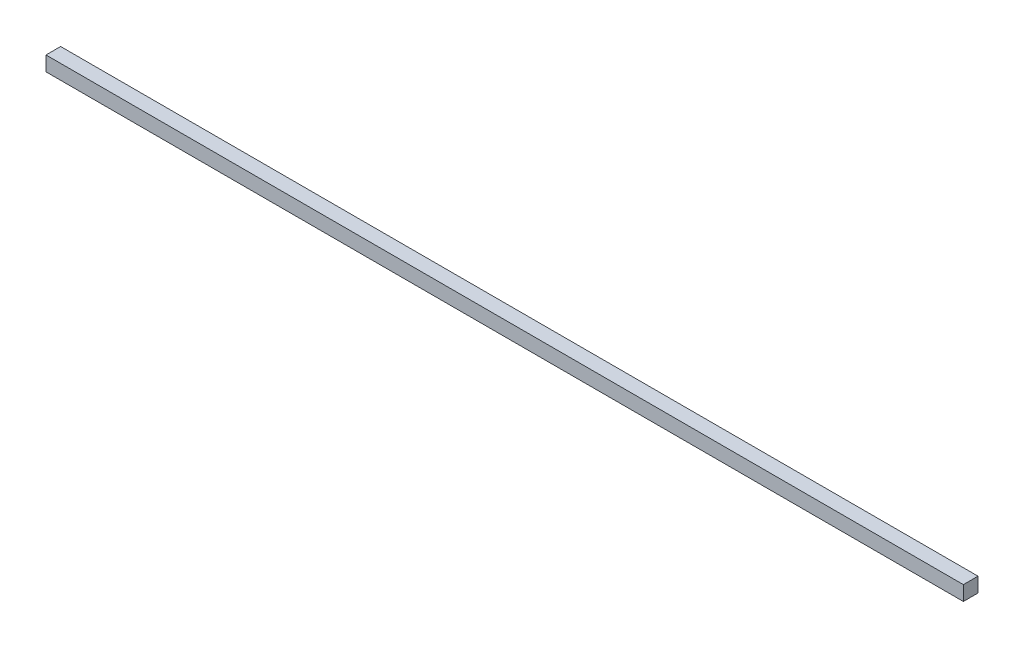
SolidWorks part; units mm, degrees
material "Plywood"
ref_plane "Front Plane" through (0, 0, 0) normal (0, 0, 1) x (1, 0, 0)
ref_plane "Top Plane" through (0, 0, 0) normal (0, 1, 0) x (1, 0, 0)
ref_plane "Right Plane" through (0, 0, 0) normal (1, 0, 0) x (0, 0, -1)
sketch "Sketch2" plane through (0, 0, 0) normal (1, 0, 0) x (0, 0, -1)
  line L1 (0, 0) -> (4.7625, 0)
  line L2 (0, 0) -> (0, 4.7625)
  line L3 (0, 4.7625) -> (4.7625, 4.7625)
  line L4 (4.7625, 0) -> (4.7625, 4.7625)
  dimension "D1" = 4.7625
extrude "Boss-Extrude1" add sketch "Sketch2" against normal blind 298.45
move or copy body "Body-Move/Copy1" [suppressed] bodies to move or copy 101 parameters "D1"=0, "D2"=0, "D3"=0
move or copy body "Body-Move/Copy2" [suppressed] bodies to move or copy 102 parameters "D1"=0, "D2"=0, "D3"=0
move or copy body "Body-Move/Copy3" [suppressed] bodies to move or copy 103 parameters "D1"=0, "D2"=0, "D3"=0
